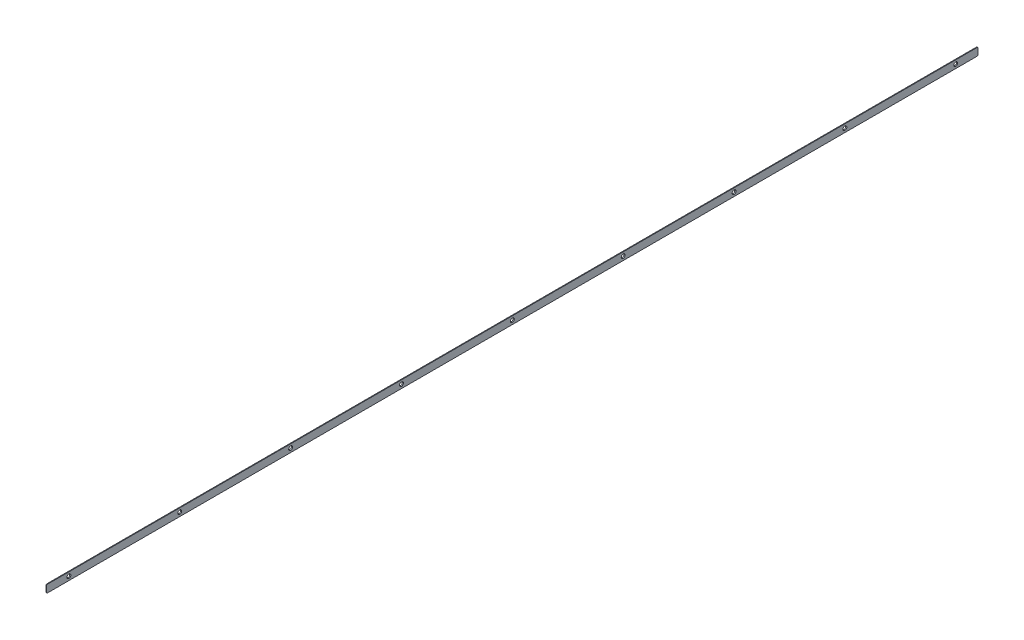
SolidWorks part; units mm, degrees
material "6061-T6 (SS)"
ref_plane "Front Plane" through (0, 0, 0) normal (0, 0, 1) x (1, 0, 0)
ref_plane "Top Plane" through (0, 0, 0) normal (0, 1, 0) x (1, 0, 0)
ref_plane "Right Plane" through (0, 0, 0) normal (1, 0, 0) x (0, 0, -1)
sketch "Sketch1" plane through (0, 0, 0) normal (1, 0, 0) x (0, 0, -1)
  line L1 (-523, 4.2705) -> (523, 4.2705)
  line L2 (-523, 4.2705) -> (-523, -4.2705)
  line L3 (-523, -4.2705) -> (523, -4.2705)
  line L4 (523, 4.2705) -> (523, -4.2705)
  line L5 (-523, 4.2705) -> (523, -4.2705) construction
  line L6 (-523, -4.2705) -> (523, 4.2705) construction
  point P0 (0, 0)
  dimension "D1" = 8.541
  dimension "D2" = 1046
extrude "Boss-Extrude1" add sketch "Sketch1" along normal blind 0.762
fillet "Fillet1" [suppressed] radius 8
hole_wizard "CSK for #2 Flat Head Machine Screw1" positions "Sketch3" profile "Sketch2" countersink size "#2" standard "ANSI Inch" end condition through all
sketch "Sketch3" plane through (0.762, 0, 0) normal (1, 0, 0) x (0, 0, -1)
  line L0 (-523, 0) -> (-536.4659, 0) construction
  line L1 (-523, 4.2705) -> (-523, -4.2705) construction
  point P0 (-498, 0)
  dimension "D1" = 25
sketch "Sketch2" plane through (0.762, 0, 498) normal (0, 1, 0) x (0, 0, -1)
  line L0 (0, 0) -> (0, 0.762)
  line L1 (0, 0.762) -> (1.2192, 0.762)
  line L2 (1.2192, 0.762) -> (1.2192, 1.1103)
  line L3 (1.2192, 1.1103) -> (2.1844, 0)
  line L5 (2.1844, 0) -> (0, 0)
  line L6 (-1.2192, 1.1103) -> (-2.1844, 0) construction
  line L11 (0, -6.35) -> (0, 107.95) construction
  dimension "Thru Hole Dia." = 2.4384
  dimension "Thru Hole Depth" = 0.762
  dimension "Near C'Sink Dia." = 4.3688
  dimension "Near C'Sink Angle" = 82
pattern_linear "LPattern1" count 9 spacing 124.5 along (0, 0, -1) of "CSK for #2 Flat Head Machine Screw1"
fillet "Fillet2" radius 1 4 edges at (0.381, 4.2705, -523) (0.381, -4.2705, -523) (0.381, -4.2705, 523) (0.381, 4.2705, 523)
